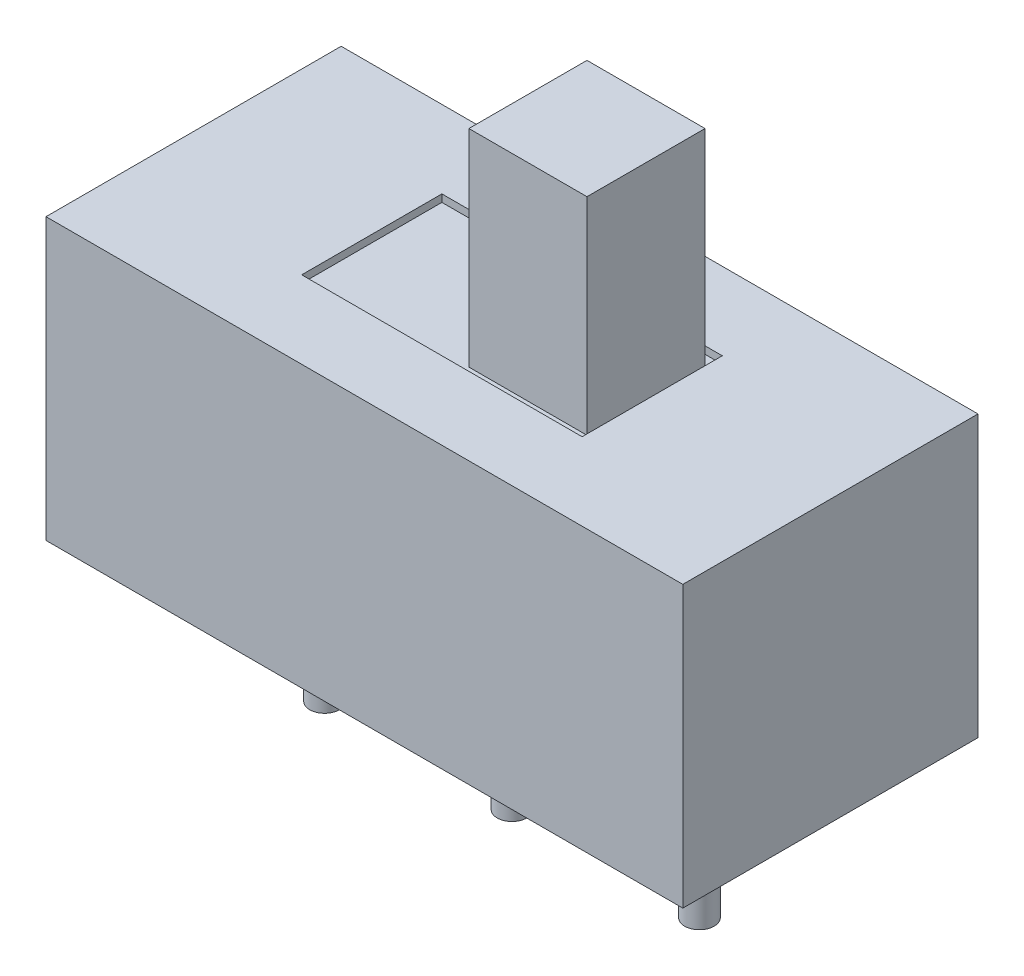
SolidWorks part; units mm, degrees
ref_plane "Спереди" through (0, 0, 0) normal (0, 0, 1) x (1, 0, 0)
ref_plane "Сверху" through (0, 0, 0) normal (0, 1, 0) x (1, 0, 0)
ref_plane "Справа" through (0, 0, 0) normal (1, 0, 0) x (0, 0, -1)
sketch "Эскиз1" plane through (0, 0, 0) normal (0, 1, 0) x (1, 0, 0)
  line L1 (-4.315, 2) -> (4.315, 2)
  line L2 (-4.315, 2) -> (-4.315, -2)
  line L3 (-4.315, -2) -> (4.315, -2)
  line L4 (4.315, 2) -> (4.315, -2)
  line L5 (-4.315, 2) -> (4.315, -2) construction
  line L6 (-4.315, -2) -> (4.315, 2) construction
  point P0 (0, 0)
  dimension "D1" = 8.63
  dimension "D2" = 4
extrude "Бобышка-Вытянуть1" add sketch "Эскиз1" along normal blind 3.8
sketch "Эскиз2" plane through (0, 3.8, 0) normal (0, 1, 0) x (1, 0, 0)
  line L1 (-1.9, 0.95) -> (1.9, 0.95)
  line L2 (-1.9, 0.95) -> (-1.9, -0.95)
  line L3 (-1.9, -0.95) -> (1.9, -0.95)
  line L4 (1.9, 0.95) -> (1.9, -0.95)
  line L5 (-1.9, 0.95) -> (1.9, -0.95) construction
  line L6 (-1.9, -0.95) -> (1.9, 0.95) construction
  point P0 (0, 0)
  dimension "D1" = 3.8
  dimension "D2" = 1.9
extrude "Вырез-Вытянуть1" cut sketch "Эскиз2" against normal blind 0.1
sketch "Эскиз3" plane through (0, 3.7, 0) normal (0, 1, 0) x (1, 0, 0)
  line L0 (-2.7207, 0) -> (2.9678, 0) construction
  line L2 (0.2159, 0.8) -> (1.8159, 0.8)
  line L3 (0.2159, 0.8) -> (0.2159, -0.8)
  line L4 (0.2159, -0.8) -> (1.8159, -0.8)
  line L5 (1.8159, 0.8) -> (1.8159, -0.8)
  line L6 (0.2159, 0.8) -> (1.8159, -0.8) construction
  line L7 (0.2159, -0.8) -> (1.8159, 0.8) construction
  point P3 (1.0159, 0)
  point P8 (1.0159, 0)
  dimension "D1" = 1.6
  dimension "D2" = 1.6
extrude "Бобышка-Вытянуть2" add sketch "Эскиз3" along normal blind 2.8 contours L2 L5 L4 L3
sketch "Эскиз4" plane through (0, 0, 0) normal (0, -1, 0) x (1, 0, 0)
  line L0 (-4.315, 0) -> (9.6863, 0) construction
  line L1 (-4.315, -2) -> (-4.315, 2) construction
  line L2 (0, 3.0328) -> (0, -3.4819) construction
  line L3 (-2.54, 3.176) -> (-2.54, -4.0137) construction
  line L4 (2.54, 3.0328) -> (2.54, -3.9012) construction
  circle A0 centre (-2.54, 0) radius 0.2
  circle A1 centre (0, 0) radius 0.2
  circle A2 centre (2.54, 0) radius 0.2
  point P17 (0, 0)
  point P18 (-2.54, 0.2)
  point P19 (-2.54, 0.2)
  point P20 (0, 0)
  point P21 (2.54, 0)
  point P22 (-2.54, 0.2)
  point P23 (-2.54, 0)
  dimension "D3" = 0.4
  dimension "D1" = 2.54
  dimension "D2" = 2.54
extrude "Бобышка-Вытянуть3" add sketch "Эскиз4" along normal blind 2
